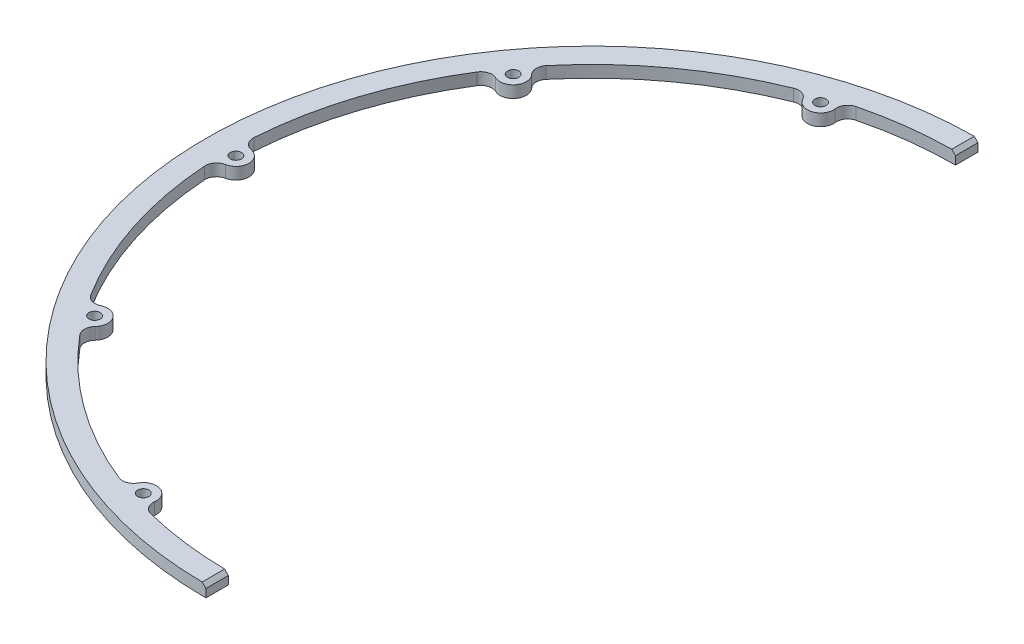
SolidWorks part; units mm, degrees
material "Acrylic (Medium-high impact)"
ref_plane "Front Plane" through (0, 0, 0) normal (0, 0, 1) x (1, 0, 0)
ref_plane "Top Plane" through (0, 0, 0) normal (0, 1, 0) x (1, 0, 0)
ref_plane "Right Plane" through (0, 0, 0) normal (1, 0, 0) x (0, 0, -1)
sketch "Sketch1" plane through (0, 0, 0) normal (0, 1, 0) x (1, 0, 0)
  line L0 (0, 103) -> (0, 97)
  line L1 (0, -97) -> (0, -103)
  arc A0 (0, 103) -> (0, -103) centre (0, 0) ccw
  arc A1 (0, 97) -> (0, -97) centre (0, 0) ccw
  dimension "D1" = 103
  dimension "D2" = 6
extrude "Boss-Extrude1" add sketch "Sketch1" along normal blind 3.18
sketch "Sketch2" plane through (0, 3.18, 0) normal (0, 1, 0) x (1, 0, 0)
  line L0 (-95, -3.5) -> (-96.9368, -3.5)
  line L1 (-95, 3.5) -> (-96.9368, 3.5)
  line L2 (-96.9368, 3.5) -> (-97.9655, 1.8589)
  line L3 (-96.9368, -3.5) -> (-97.9655, -1.8589)
  circle A2 centre (-95, 0) radius 3.5
  arc A3 (0, 97) -> (0, -97) centre (0, 0) ccw construction
  arc M4 (0, -97) -> (0, 97) centre (0, 0) cw
  dimension "D1" = 95
  dimension "D2" = 7
extrude "Boss-Extrude2" add sketch "Sketch2" against normal up to surface (3.18 mm away) contours A2 L2 M4 | A2 L1 M4 | A2 L3 M4 | A2 L0 M4 | A2 M4 | A2 M4 up to face at (-50, 0, 0)
fillet "Fillet1" radius 3 2 edges at (-96.9368, 1.59, -3.5) (-96.9368, 1.59, 3.5)
sketch "Sketch3" plane through (0, 3.18, 0) normal (0, 1, 0) x (1, 0, 0)
  circle A0 centre (-95, 0) radius 1.5
  dimension "D1" = 3
  dimension "D2" = 95
extrude "Cut-Extrude1" cut sketch "Sketch3" against normal up to next (3.18 mm away)
pattern_circular "CirPattern1" count 3 every 36 about axis through (0, 0, 0) along (0, 1, 0) of "Boss-Extrude2", "Cut-Extrude1", "Fillet1"
chamfer "Chamfer1" distance 1 angle 45 2 edges at (0, 3.18, -100) (0, 3.18, 100)
